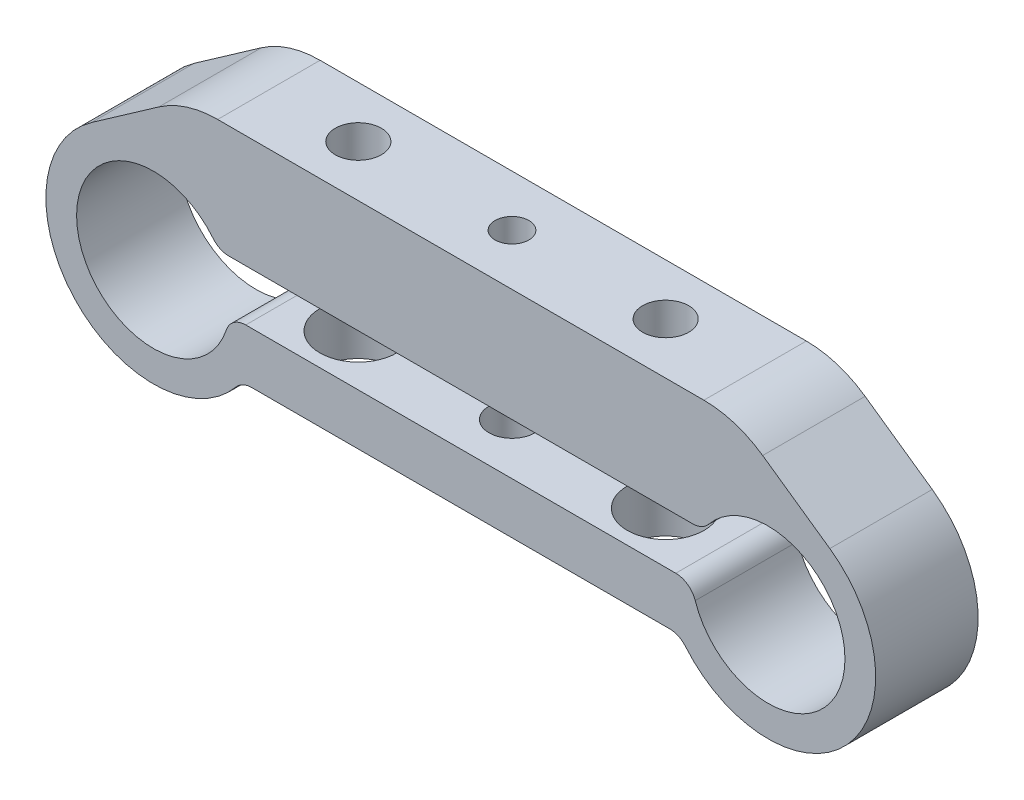
SolidWorks part; units mm, degrees
material "Сплав 2024"
ref_plane "Спереди" through (0, 0, 0) normal (0, 0, 1) x (1, 0, 0)
ref_plane "Сверху" through (0, 0, 0) normal (0, 1, 0) x (1, 0, 0)
ref_plane "Справа" through (0, 0, 0) normal (1, 0, 0) x (0, 0, -1)
sketch "Эскиз1" plane through (0, 0, 0) normal (0, 0, 1) x (1, 0, 0)
  line L0 (-31.8271, 0) -> (48.3301, 0) construction
  line L1 (-26.884, 15) -> (26.884, 15)
  line L2 (-36.0226, 8.6011) -> (-26.884, 15)
  line L3 (36.0226, 8.6011) -> (26.884, 15)
  line L4 (-23.6557, 4) -> (23.6557, 4)
  line L5 (-22.567, -1) -> (22.567, -1)
  line L6 (-21.3832, -6) -> (21.3832, -6)
  arc A0 (-23.6557, 4) -> (-22.567, -1) centre (-30, 0) ccw
  arc A1 (22.567, -1) -> (23.6557, 4) centre (30, 0) ccw
  arc A2 (-36.0226, 8.6011) -> (-21.3832, -6) centre (-30, 0) ccw
  arc A3 (21.3832, -6) -> (36.0226, 8.6011) centre (30, 0) ccw
  circle A5 centre (-30, 0) radius 7.5 construction
  circle A6 centre (-30, 0) radius 10.5 construction
  circle A7 centre (30, 0) radius 10.5 construction
  circle A8 centre (30, 0) radius 7.5 construction
  point P4 (-19.5, 0)
  point P9 (40.5, 0)
  point P12 (37.1723, 2.1928)
  point P21 (-22.8277, 2.1928)
  dimension "D1" = 15
  dimension "D2" = 15
  dimension "D3" = 30
  dimension "D4" = 60
  dimension "D5" = 3
  dimension "D6" = 15
  dimension "D8" = 35
  dimension "D9" = 35
  dimension "D10" = 11
  dimension "D11" = 5
  dimension "D12" = 5
  dimension "D7" = 3
extrude "Бобышка-Вытянуть1" add sketch "Эскиз1" along normal blind 10
sketch "Эскиз2" plane through (0, -6, 0) normal (0, -1, 0) x (1, 0, 0)
  line L0 (-21.3832, 5) -> (21.3832, 5) construction
  line L1 (-21.3832, 10) -> (-21.3832, 0) construction
  line L2 (21.3832, 10) -> (21.3832, 0) construction
  line L3 (-15, 10) -> (-15, 0) construction
  line L4 (-21.3832, 10) -> (21.3832, 10) construction
  line L5 (-21.3832, 0) -> (21.3832, 0) construction
  line L6 (15, 10) -> (15, 0) construction
  line L7 (0, 10) -> (0, 0) construction
  dimension "D1" = 15
  dimension "D2" = 15
sketch "Эскиз3" plane through (0, -6, 0) normal (0, -1, 0) x (1, 0, 0)
  line L0 (-15, 10) -> (-15, 0) construction
  line L1 (15, 10) -> (15, 0) construction
  circle A0 centre (-15, 5) radius 3.75
  circle A1 centre (15, 5) radius 3.75
  dimension "D1" = 7.5
  dimension "D2" = 7.5
extrude "Вырез-Вытянуть1" cut sketch "Эскиз3" against normal up to next
hole_wizard "Отверстие с зазором M41" positions "Эскиз5" profile "Эскиз4" hole size "M4" standard "Ansi Metric" end condition through all
sketch "Эскиз5" plane through (0, 4, 0) normal (0, -1, 0) x (-1, 0, 0)
  line L0 (15, -10) -> (15, 0) construction
  point P0 (-15, -5)
  point P3 (15, -5)
sketch "Эскиз4" plane through (15, 4, 5) normal (1, 0, 0) x (0, 0, -1)
  line L0 (0, 0) -> (0, 11)
  line L1 (0, 11) -> (2.25, 11)
  line L2 (2.25, 11) -> (2.25, 0)
  line L5 (2.25, 0) -> (0, 0)
  line L11 (0, -6.35) -> (0, 107.95) construction
  dimension "Диаметр сквозного отверстия" = 4.5
  dimension "Глубина сквозного отверстия" = 11
hole_wizard "Отверстие с зазором M42" positions "Эскиз7" profile "Эскиз8" hole size "M4" standard "Ansi Metric" end condition up to next
sketch "Эскиз7" plane through (0, -6, 0) normal (0, -1, 0) x (-1, 0, 0)
  line L0 (21.3832, -5) -> (-21.3832, -5) construction
  point P0 (0, -5)
sketch "Эскиз8" plane through (0, -6, 5) normal (1, 0, 0) x (0, 0, -1)
  line L0 (0, 0) -> (0, 5)
  line L1 (0, 5) -> (2.25, 5)
  line L2 (2.25, 5) -> (2.25, 0)
  line L5 (2.25, 0) -> (0, 0)
  line L11 (0, -6.35) -> (0, 107.95) construction
  dimension "Диаметр сквозного отверстия" = 4.5
  dimension "Глубина сквозного отверстия" = 5
hole_wizard "Отверстие обработанное метчиком M4x0.71" positions "Эскиз10" profile "Эскиз9" tap size "M4x0.7" standard "Ansi Metric" end condition through all
sketch "Эскиз10" plane through (0, 4, 0) normal (0, -1, 0) x (-1, 0, 0)
  line L0 (21.3832, -5) -> (-21.3832, -5) construction
  point P0 (0, -5)
sketch "Эскиз9" plane through (0, 4, 5) normal (1, 0, 0) x (0, 0, -1)
  line L0 (0, 0) -> (0, 11)
  line L1 (0, 11) -> (1.65, 11)
  line L2 (1.65, 11) -> (1.65, 0)
  line L5 (1.65, 0) -> (0, 0)
  line L11 (0, -6.35) -> (0, 107.95) construction
  dimension "Диаметр проходного сверла" = 3.3
  dimension "Глубина проходного сверла" = 11
cosmetic thread "Отверстие резьбы1" parameters "D2"=4
fillet "Скругление1" radius 10 2 edges at (-26.884, 15, 5) (26.884, 15, 5)
fillet "Скругление2" radius 2 6 edges at (21.3832, -6, 5) (-21.3832, -6, 5) (-22.567, -1, 5) (-23.6557, 4, 5) (22.567, -1, 5) (23.6557, 4, 5)
